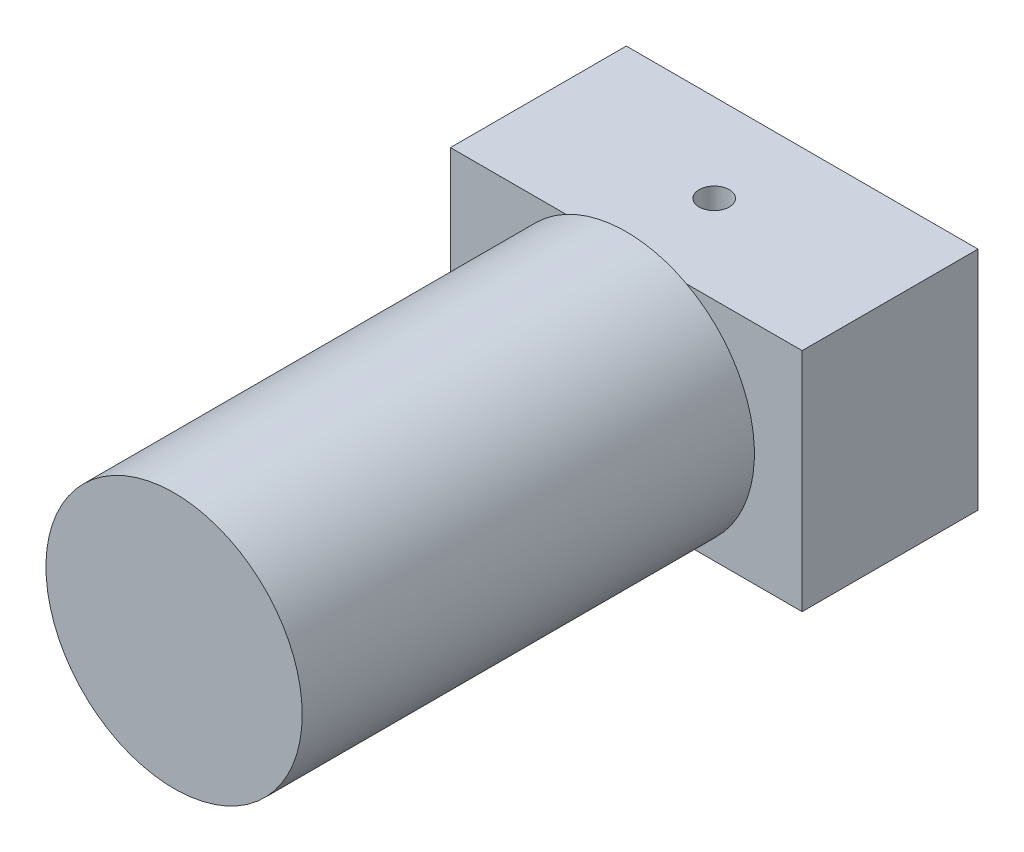
SolidWorks part; units mm, degrees
ref_plane "Front Plane" through (0, 0, 0) normal (0, 0, 1) x (1, 0, 0)
ref_plane "Top Plane" through (0, 0, 0) normal (0, 1, 0) x (1, 0, 0)
ref_plane "Right Plane" through (0, 0, 0) normal (1, 0, 0) x (0, 0, -1)
sketch "Sketch1" plane through (0, 0, 0) normal (0, 0, 1) x (1, 0, 0)
  line L1 (-35, -22.5) -> (35, -22.5)
  line L2 (-35, -22.5) -> (-35, 22.5)
  line L3 (-35, 22.5) -> (35, 22.5)
  line L4 (35, -22.5) -> (35, 22.5)
  line L5 (-35, -22.5) -> (35, 22.5) construction
  line L6 (-35, 22.5) -> (35, -22.5) construction
  point P0 (0, 0)
  dimension "D1" = 70
  dimension "D2" = 45
extrude "Boss-Extrude1" add sketch "Sketch1" along normal blind 35
sketch "Sketch2" plane through (0, 0, 35) normal (0, 0, 1) x (1, 0, 0)
  circle A0 centre (0, 0) radius 25.5
  dimension "D1" = 51
extrude "Boss-Extrude2" add sketch "Sketch2" along normal blind 90
sketch "Sketch3" plane through (0, 22.5, 0) normal (0, 1, 0) x (1, 0, 0)
  line L0 (-35, 0) -> (35, -35) construction
  circle A0 centre (0, -17.5) radius 3
  dimension "D1" = 6
extrude "Cut-Extrude1" cut sketch "Sketch3" against normal blind 10
